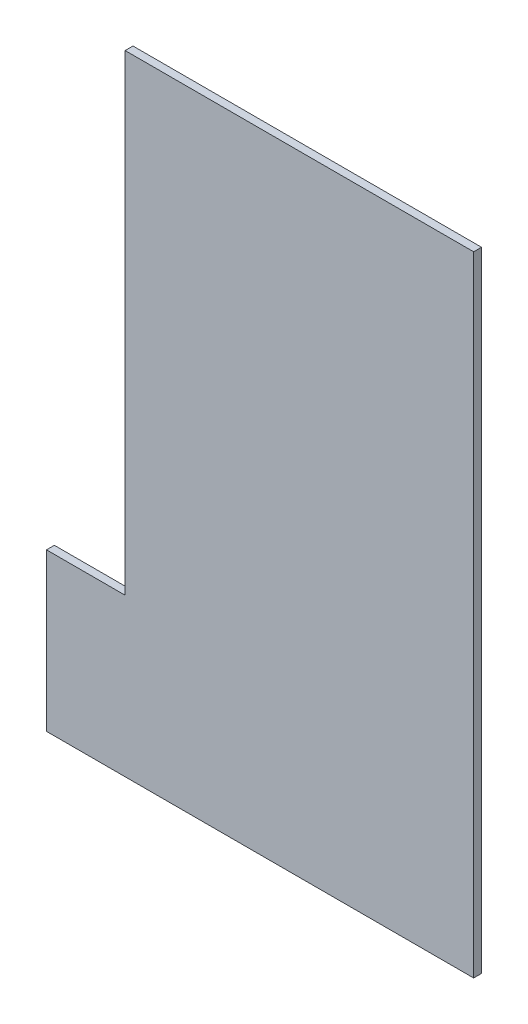
SolidWorks part; units mm, degrees
ref_plane "Plan de face" through (0, 0, 0) normal (0, 0, 1) x (1, 0, 0)
ref_plane "Plan de dessus" through (0, 0, 0) normal (0, 1, 0) x (1, 0, 0)
ref_plane "Plan de droite" through (0, 0, 0) normal (1, 0, 0) x (0, 0, -1)
sketch "Esquisse1" plane through (0, 0, 0) normal (0, 0, 1) x (1, 0, 0)
  line L1 (-62.9102, 49.3173) -> (70.0898, 49.3173)
  line L2 (-62.9102, 49.3173) -> (-62.9102, -130.6827)
  line L3 (-62.9102, -190.6827) -> (70.0898, -190.6827)
  line L4 (70.0898, 49.3173) -> (70.0898, -190.6827)
  line L5 (-62.9102, -190.6827) -> (-92.9102, -190.6827)
  line L7 (-62.9102, -130.6827) -> (-92.9102, -130.6827)
  line L8 (-92.9102, -190.6827) -> (-92.9102, -130.6827)
  dimension "D1" = 133
  dimension "D2" = 240
  dimension "D3" = 30
  dimension "D4" = 60
extrude "Boss.-Extru.1" add sketch "Esquisse1" along normal blind 3
equation "\"D1@Esquisse1\"=\"LargeurBoite\" - \"LargeurGauche\" + \"EpaisseurPlaque\""
equation "\"ProfondeurBoite\"=460"
equation "\"LongueurSyphon\"=270"
equation "\"LargeurSyphon\"=120"
equation "\"EpaisseurPlaque\"= 3"
equation "\"HauteurCoteDroit\"= 490"
equation "\"HauteurCoteGauche\"= 540"
equation "\"HauteurSolSyphon\"= 300"
equation "\"HauteurSyphon\"=\"HauteurCoteGauche\"-\"HauteurSolSyphon\""
equation "\"D2@Esquisse1\" = \"HauteurSyphon\""
equation "\"LargeurDroite\"=10"
equation "\"LargeurGauche\"=150"
equation "\"LargeurBoite\"= \"LargeurDroite\" + \"LargeurGauche\" + \"LargeurSyphon\""
